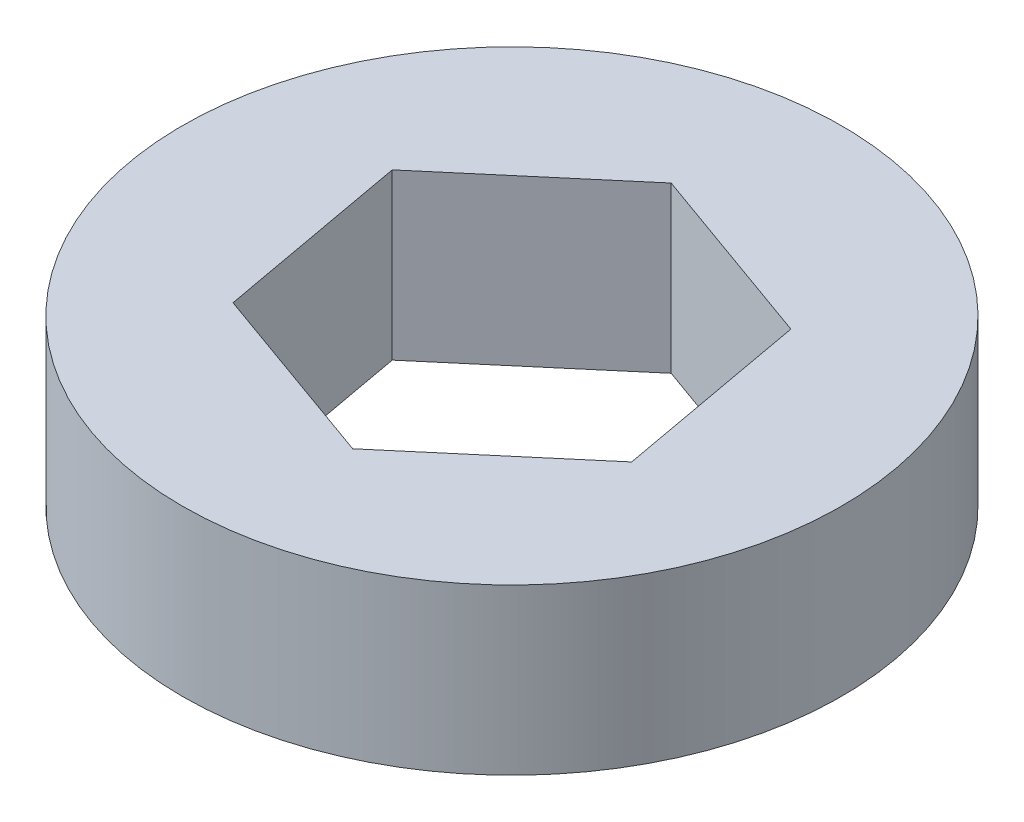
SolidWorks part; units mm, degrees
ref_plane "Front Plane" through (0, 0, 0) normal (0, 0, 1) x (1, 0, 0)
ref_plane "Top Plane" through (0, 0, 0) normal (0, 1, 0) x (1, 0, 0)
ref_plane "Right Plane" through (0, 0, 0) normal (1, 0, 0) x (0, 0, -1)
sketch "Sketch1" plane through (0, 0, 0) normal (0, 1, 0) x (1, 0, 0)
  circle A0 centre (0, 0) radius 12.7
extrude "Boss-Extrude1" add sketch "Sketch1" along normal blind 6.35
sketch "Sketch2" plane through (0, 0, 0) normal (0, 1, 0) x (1, 0, 0)
  line L1 (-1.3664, 7.5022) -> (-7.1803, 2.5678)
  line L2 (-7.1803, 2.5678) -> (-5.8139, -4.9344)
  line L3 (-5.8139, -4.9344) -> (1.3664, -7.5022)
  line L4 (1.3664, -7.5022) -> (7.1803, -2.5678)
  line L5 (7.1803, -2.5678) -> (5.8139, 4.9344)
  line L6 (5.8139, 4.9344) -> (-1.3664, 7.5022)
  circle A0 centre (0, 0) radius 6.604 construction
extrude "Cut-Extrude1" cut sketch "Sketch2" along normal up to surface (6.35 mm away) up to face at (0, 6.35, 12.7)
